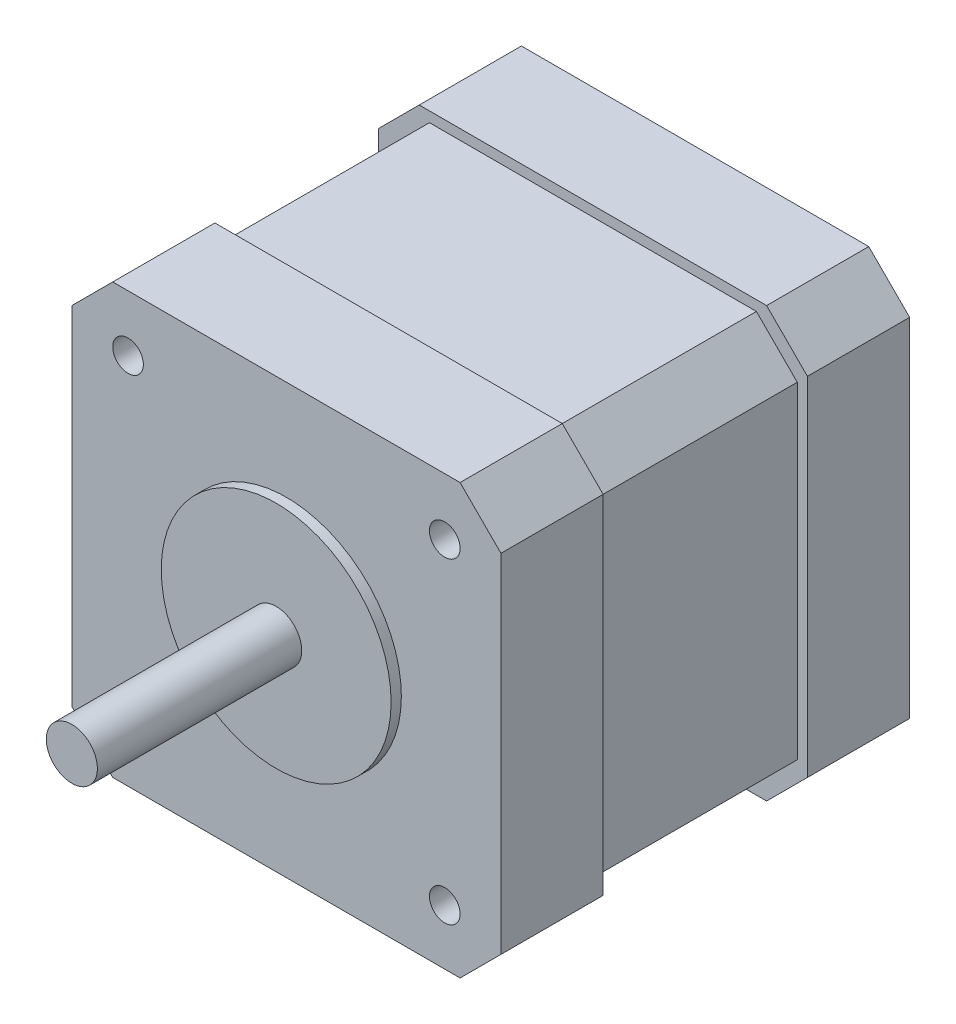
SolidWorks part; units mm, degrees
ref_plane "Front Plane" through (0, 0, 0) normal (0, 0, 1) x (1, 0, 0)
ref_plane "Top Plane" through (0, 0, 0) normal (0, 1, 0) x (1, 0, 0)
ref_plane "Right Plane" through (0, 0, 0) normal (1, 0, 0) x (0, 0, -1)
sketch "Sketch1" plane through (0, 0, 0) normal (0, 0, 1) x (1, 0, 0)
  line L1 (-21, 21) -> (21, 21)
  line L2 (-21, 21) -> (-21, -21)
  line L3 (-21, -21) -> (21, -21)
  line L4 (21, 21) -> (21, -21)
  line L5 (-21, 21) -> (21, -21) construction
  line L6 (-21, -21) -> (21, 21) construction
  point P0 (0, 0)
  dimension "D1" = 42
  dimension "D2" = 42
extrude "Boss-Extrude1" add sketch "Sketch1" along normal blind 10
sketch "Sketch2" plane through (0, 0, 10) normal (0, 0, 1) x (1, 0, 0)
  line L1 (-20, 20) -> (20, 20)
  line L2 (-20, 20) -> (-20, -20)
  line L3 (-20, -20) -> (20, -20)
  line L4 (20, 20) -> (20, -20)
  line L5 (-20, 20) -> (20, -20) construction
  line L6 (-20, -20) -> (20, 20) construction
  point P0 (0, 0)
  dimension "D1" = 40
  dimension "D2" = 40
extrude "Boss-Extrude2" add sketch "Sketch2" along normal blind 20
sketch "Sketch3" plane through (0, 0, 30) normal (0, 0, 1) x (1, 0, 0)
  line L1 (-21, 21) -> (21, 21)
  line L2 (-21, 21) -> (-21, -21)
  line L3 (-21, -21) -> (21, -21)
  line L4 (21, 21) -> (21, -21)
  line L5 (-21, 21) -> (21, -21) construction
  line L6 (-21, -21) -> (21, 21) construction
  point P0 (0, 0)
  dimension "D1" = 42
  dimension "D2" = 42
extrude "Boss-Extrude3" add sketch "Sketch3" along normal blind 10
sketch "Sketch4" plane through (0, 0, 40) normal (0, 0, 1) x (1, 0, 0)
  circle A0 centre (0, 0) radius 11.25
  dimension "D1" = 22.5
extrude "Boss-Extrude4" add sketch "Sketch4" along normal blind 1
chamfer "Chamfer1" distance 4 angle 45 12 edges at (-21, -21, 35) (-20, -20, 20) (-21, -21, 5) (21, -21, 35) (20, -20, 20) (21, -21, 5) (21, 21, 35) (20, 20, 20) (21, 21, 5) (-21, 21, 35) (-20, 20, 20) (-21, 21, 5)
sketch "Sketch5" plane through (0, 0, 41) normal (0, 0, 1) x (1, 0, 0)
  circle A0 centre (0, 0) radius 2.5
  dimension "D1" = 5
extrude "Boss-Extrude5" add sketch "Sketch5" along normal blind 20
sketch "Sketch6" plane through (0, 0, 40) normal (0, 0, 1) x (1, 0, 0)
  circle A0 centre (-15.5, -15.5) radius 1.5
  circle A1 centre (-15.5, 15.5) radius 1.5
  circle A2 centre (15.5, 15.4179) radius 1.5
  circle A3 centre (15.5, -15.5821) radius 1.5
  dimension "D8" = 3
  dimension "D9" = 3
  dimension "D10" = 3
  dimension "D11" = 3
  dimension "D1" = 31
  dimension "D2" = 31
  dimension "D3" = 31
  dimension "D4" = 31
  dimension "D5" = 15.5
  dimension "D6" = 15.5
  dimension "D7" = 15.5
extrude "Cut-Extrude1" cut sketch "Sketch6" against normal blind 40
